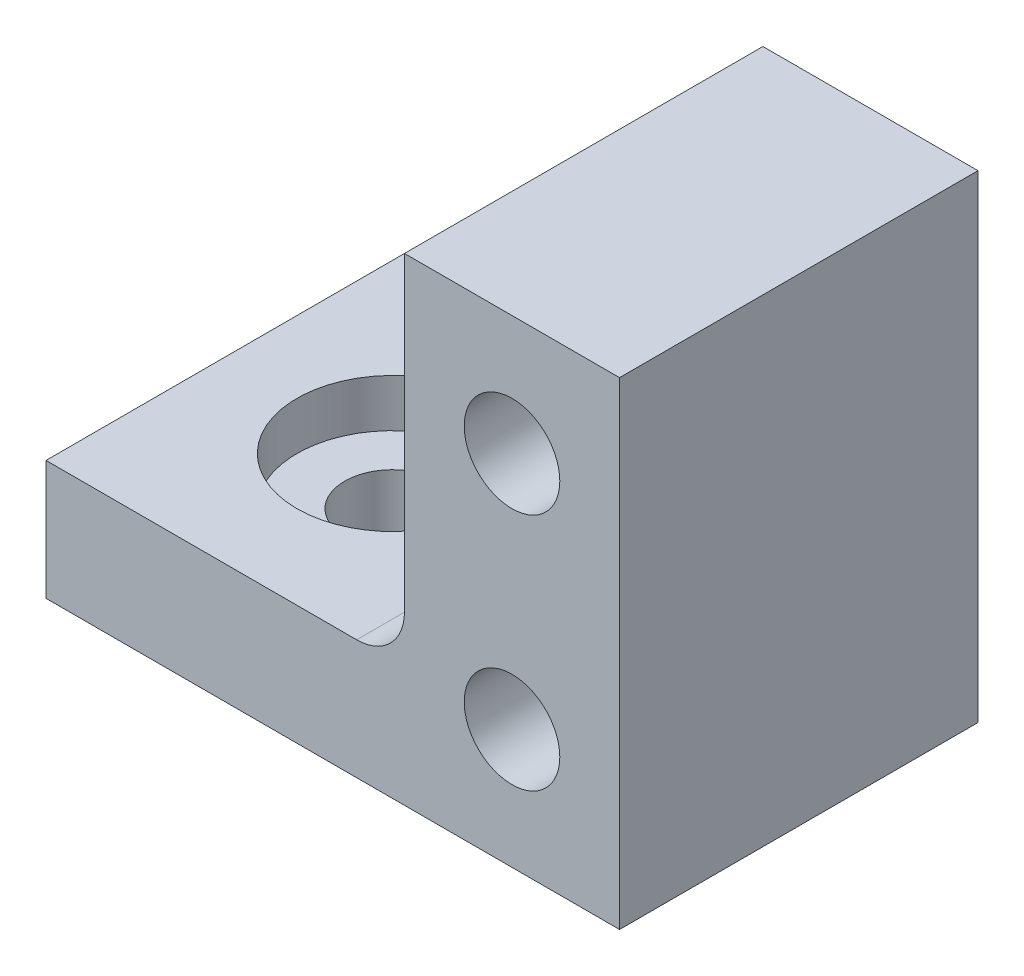
SolidWorks part; units mm, degrees
ref_plane "Front Plane" through (0, 0, 0) normal (0, 0, 1) x (1, 0, 0)
ref_plane "Top Plane" through (0, 0, 0) normal (0, 1, 0) x (1, 0, 0)
ref_plane "Right Plane" through (0, 0, 0) normal (1, 0, 0) x (0, 0, -1)
sketch "Sketch1" plane through (0, 0, 0) normal (0, 1, 0) x (1, 0, 0)
  line L1 (-12, 7.5) -> (12, 7.5)
  line L2 (-12, 7.5) -> (-12, -7.5)
  line L3 (-12, -7.5) -> (12, -7.5)
  line L4 (12, 7.5) -> (12, -7.5)
  line L5 (-12, 7.5) -> (12, -7.5) construction
  line L6 (-12, -7.5) -> (12, 7.5) construction
  point P0 (0, 0)
  dimension "D1" = 15
  dimension "D2" = 24
extrude "Boss-Extrude2" add sketch "Sketch1" along normal blind 5 contours L1 L4 L3 L2
ref_plane "Plane5" through (0, 5, 0) normal (0, 1, 0) x (1, 0, 0)
sketch "Sketch8" plane through (0, 5, 0) normal (0, 1, 0) x (1, 0, 0)
  line L0 (12, 7.5) -> (3, 7.5)
  line L1 (-12, 7.5) -> (12, 7.5) construction
  line L2 (3, 7.5) -> (3, -7.5)
  line L3 (-12, -7.5) -> (12, -7.5) construction
  line L4 (3, -7.5) -> (12, -7.5)
  line L5 (12, -7.5) -> (12, 7.5)
  dimension "D1" = 9
extrude "Boss-Extrude3" add sketch "Sketch8" along normal blind 15
sketch "Sketch9" plane through (0, 5, 0) normal (0, 1, 0) x (1, 0, 0)
  line L0 (-12, -7.5) -> (3, -7.5) construction
  circle A0 centre (-5, 0) radius 4
  dimension "D1" = 8
  dimension "D2" = 7.5
  dimension "D3" = 5
sketch "Sketch10" plane through (0, 5, 0) normal (0, 1, 0) x (1, 0, 0)
  circle A0 centre (-5, 0) radius 2
  dimension "D1" = 4
extrude "Cut-Extrude3" cut sketch "Sketch10" against normal up to next
extrude "Cut-Extrude4" cut sketch "Sketch9" against normal blind 2
ref_plane "Plane6" through (0, 0, 7.5) normal (0, 0, 1) x (1, 0, 0)
sketch "Sketch11" plane through (0, 0, 7.5) normal (0, 0, 1) x (1, 0, 0)
  line L0 (3, 20) -> (12, 20) construction
  line L2 (-12, 0) -> (12, 0) construction
  line L3 (12, 20) -> (12, 0) construction
  circle A0 centre (7.5, 15) radius 2
  circle A1 centre (7.5, 5) radius 2
  dimension "D1" = 4
  dimension "D2" = 4
  dimension "D3" = 5
  dimension "D4" = 10
  dimension "D5" = 5
  dimension "D6" = 4.5
extrude "Cut-Extrude5" cut sketch "Sketch11" against normal up to next contours A0 | A1
fillet "Fillet4" radius 2 1 edges at (3, 5, 0)
